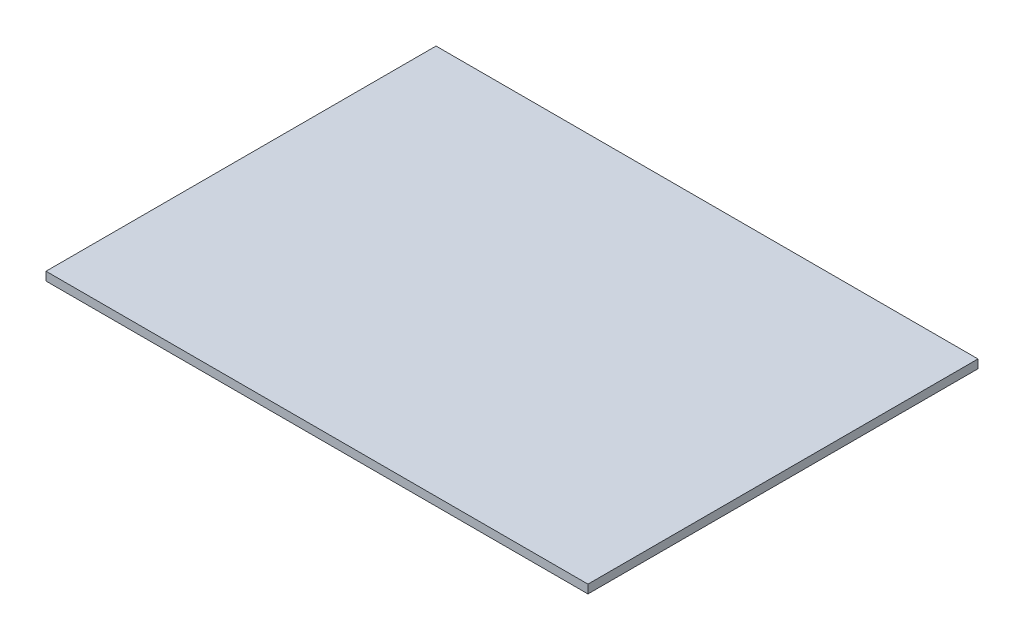
SolidWorks part; units mm, degrees
ref_plane "Front Plane" through (0, 0, 0) normal (0, 0, 1) x (1, 0, 0)
ref_plane "Top Plane" through (0, 0, 0) normal (0, 1, 0) x (1, 0, 0)
ref_plane "Right Plane" through (0, 0, 0) normal (1, 0, 0) x (0, 0, -1)
sketch "Sketch1" plane through (0, 0, 0) normal (0, 1, 0) x (1, 0, 0)
  line L1 (-58.7424, 22.084) -> (4.7576, 22.084)
  line L2 (-58.7424, 22.084) -> (-58.7424, -23.616)
  line L3 (-58.7424, -23.616) -> (4.7576, -23.616)
  line L4 (4.7576, 22.084) -> (4.7576, -23.616)
  dimension "D1" = 63.5
  dimension "D2" = 45.7
extrude "Boss-Extrude1" add sketch "Sketch1" along normal blind 1
sketch "Sketch2" plane through (-2.764, 1, 2.123) normal (0, 1, 0) x (1, 0, 0)
  line L1 (-54.7968, 20.576) -> (2.3532, 20.576)
  line L2 (-54.7968, 20.576) -> (-54.7968, -18.774)
  line L3 (-54.7968, -18.774) -> (2.3532, -18.774)
  line L4 (2.3532, 20.576) -> (2.3532, -18.774)
  dimension "D1" = 57.15
  dimension "D2" = 39.35
